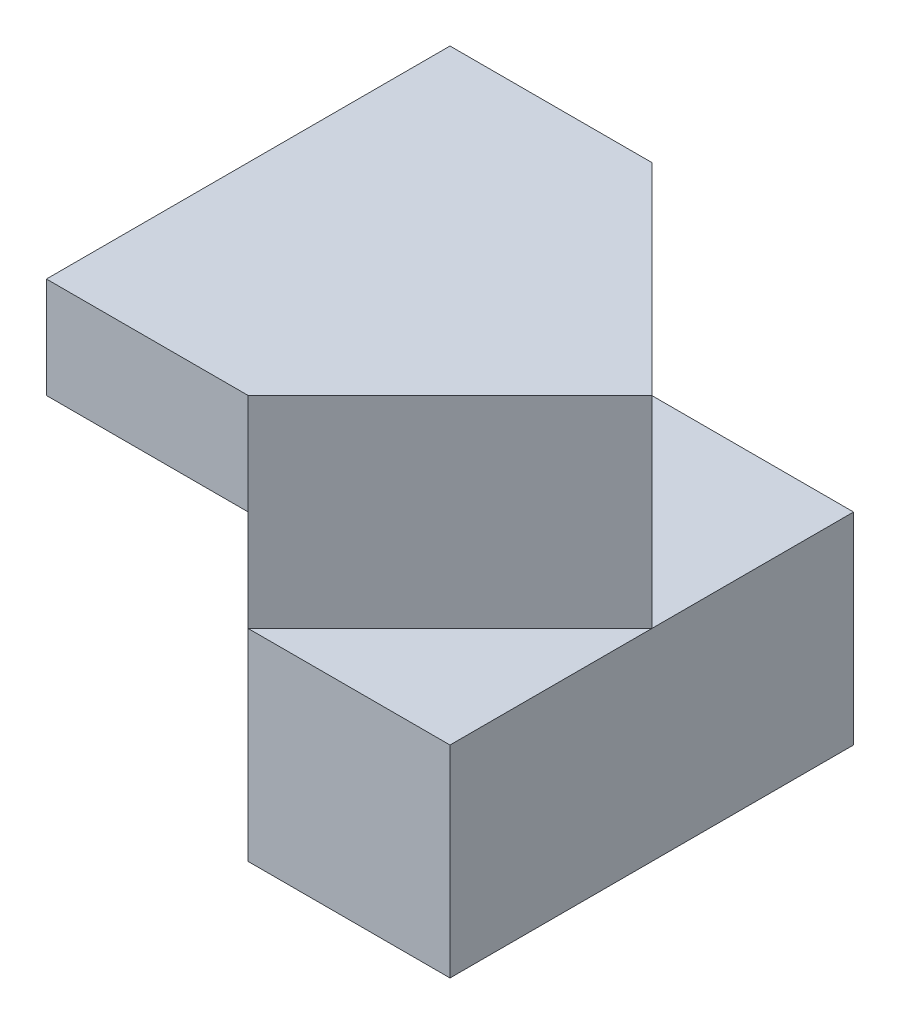
SolidWorks part; units mm, degrees
ref_plane "Front Plane" through (0, 0, 0) normal (0, 0, 1) x (1, 0, 0)
ref_plane "Top Plane" through (0, 0, 0) normal (0, 1, 0) x (1, 0, 0)
ref_plane "Right Plane" through (0, 0, 0) normal (1, 0, 0) x (0, 0, -1)
sketch "Sketch5" plane through (0, 0, 0) normal (0, 1, 0) x (1, 0, 0)
  line L1 (0, 0) -> (4, 0)
  line L2 (0, 0) -> (0, 4)
  line L3 (0, 4) -> (4, 4)
  line L4 (4, 0) -> (4, 4)
  dimension "D1" = 4
  dimension "D2" = 4
extrude "Boss-Extrude2" add sketch "Sketch5" along normal blind 4
sketch "Sketch7" plane through (0, 0, 0) normal (-1, 0, 0) x (0, 0, 1)
  line L0 (0, 3) -> (-2, 3)
  line L1 (0, 4) -> (0, 0) construction
  line L2 (-2, 3) -> (-2, 0)
  line L3 (-4, 0) -> (0, 0) construction
  line L4 (-2, 0) -> (0, 0)
  line L5 (0, 0) -> (0, 3)
  dimension "D1" = 3
extrude "Cut-Extrude5" cut sketch "Sketch7" against normal blind 2
sketch "Sketch11" plane through (0, 4, 0) normal (0, 1, 0) x (1, 0, 0)
  line L0 (2, 0) -> (4, 2)
  line L1 (0, 0) -> (4, 0) construction
  line L2 (4, 0) -> (4, 4) construction
  line L3 (4, 2) -> (4, 0)
  line L4 (4, 0) -> (2, 0)
extrude "Cut-Extrude8" cut sketch "Sketch11" against normal blind 2
sketch "Sketch13" plane through (0, 4, 0) normal (0, 1, 0) x (1, 0, 0)
  line L0 (2, 4) -> (4, 2)
  line L1 (4, 4) -> (0, 4) construction
  line L2 (4, 2) -> (4, 4)
  line L3 (4, 4) -> (2, 4)
extrude "Cut-Extrude10" cut sketch "Sketch13" against normal blind 2
sketch "Sketch14" plane through (0, 0, 0) normal (-1, 0, 0) x (0, 0, 1)
  line L0 (-2, 3) -> (-4, 0)
  line L1 (-4, 0) -> (-4, 4)
  line L2 (-4, 4) -> (-2, 3)
  line L3 (-2, 3) -> (-4, 3)
  line M1 (-4, 0) -> (-2, 0)
  line M2 (-2, 0) -> (-2, 3)
extrude "Cut-Extrude13" cut sketch "Sketch14" against normal blind 2 contours L0 M2 M1
